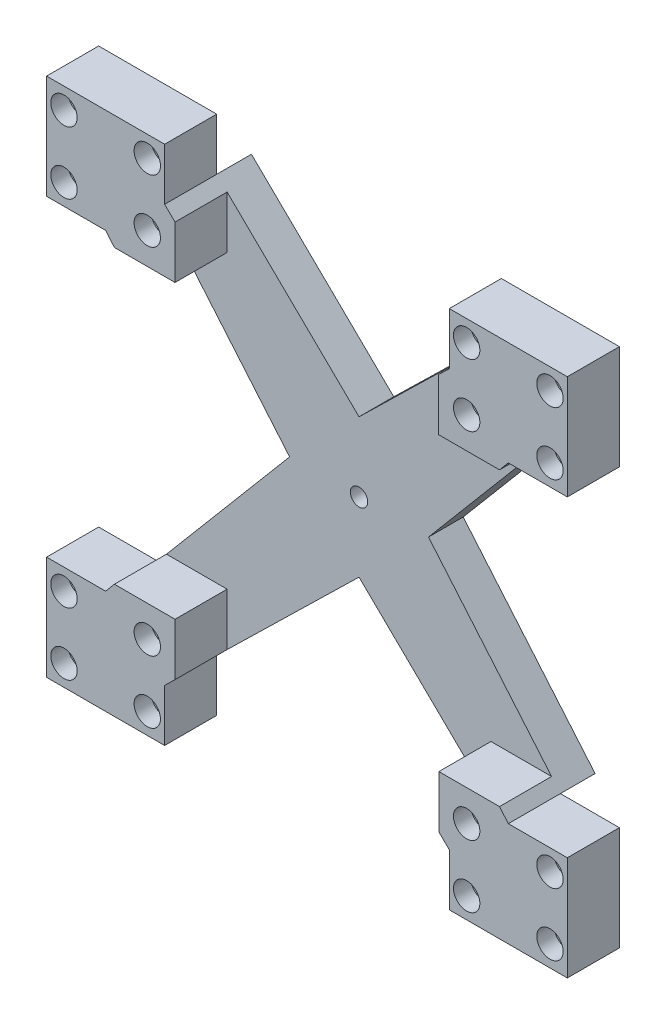
SolidWorks part; units mm, degrees
ref_plane "Front Plane" through (0, 0, 0) normal (0, 0, 1) x (1, 0, 0)
ref_plane "Top Plane" through (0, 0, 0) normal (0, 1, 0) x (1, 0, 0)
ref_plane "Right Plane" through (0, 0, 0) normal (1, 0, 0) x (0, 0, -1)
sketch "Sketch1" plane through (0, 0, 0) normal (0, 0, 1) x (1, 0, 0)
  line L1 (-75, -75) -> (75, -75)
  line L2 (-75, -75) -> (-75, 75)
  line L3 (-75, 75) -> (75, 75)
  line L4 (75, -75) -> (75, 75)
  line L5 (-75, -75) -> (75, 75) construction
  line L6 (-75, 75) -> (75, -75) construction
  point P0 (0, 0)
  dimension "D1" = 150
  dimension "D2" = 150
extrude "Boss-Extrude1" add sketch "Sketch1" along normal blind 15
sketch "Sketch2" plane through (0, 0, 15) normal (0, 0, 1) x (1, 0, 0)
  line L0 (-41, 60) -> (0, 20)
  line L1 (-75, 75) -> (-41, 75)
  line L2 (-75, 75) -> (-75, 45)
  line L3 (-75, 45) -> (-41, 45)
  line L4 (-41, 75) -> (-41, 45)
  line L5 (75, 75) -> (41, 75)
  line L6 (75, 75) -> (75, 45)
  line L7 (75, 45) -> (41, 45)
  line L8 (41, 75) -> (41, 45)
  line L9 (-75, -75) -> (-41, -75)
  line L10 (-75, -75) -> (-75, -45)
  line L11 (-75, -45) -> (-41, -45)
  line L12 (-41, -75) -> (-41, -45)
  line L13 (75, -75) -> (41, -75)
  line L14 (75, -75) -> (75, -45)
  line L15 (75, -45) -> (41, -45)
  line L16 (41, -75) -> (41, -45)
  line L17 (-20, -20) -> (20, -20)
  line L18 (-20, -20) -> (-20, 20)
  line L19 (-20, 20) -> (20, 20)
  line L20 (20, -20) -> (20, 20)
  line L21 (-20, -20) -> (20, 20) construction
  line L22 (-20, 20) -> (20, -20) construction
  line L23 (0, 20) -> (41, 60)
  line L24 (-58, -45) -> (-20, 0)
  line L25 (-20, 0) -> (-58, 45)
  line L26 (-41, -60) -> (0, -20)
  line L27 (0, -20) -> (41, -60)
  line L28 (58, 45) -> (20, 0)
  line L29 (20, 0) -> (58, -45)
  point P20 (0, 0)
  line M15 (75, -75) -> (75, 75)
  line M16 (75, 75) -> (-75, 75)
  line M17 (-75, 75) -> (-75, -75)
  line M18 (-75, -75) -> (75, -75)
  dimension "D1" = 34
  dimension "D2" = 30
  dimension "D3" = 34
  dimension "D4" = 30
  dimension "D5" = 30
  dimension "D6" = 30
  dimension "D7" = 34
  dimension "D8" = 34
  dimension "D9" = 40
  dimension "D10" = 40
extrude "Cut-Extrude1" cut sketch "Sketch2" against normal blind 15 contours L0 L23 L8 L4 M16 | L24 L25 L3 L11 M17 | L28 L29 L15 L7 M15 | L27 L26 L12 L16 M18
sketch "Sketch3" plane through (0, 0, 15) normal (0, 0, 1) x (1, 0, 0)
  line L0 (-58, 45.0694) -> (-20, 0)
  line L1 (-41, -75) -> (-75, -75)
  line L2 (-41, -75) -> (-41, -45)
  line L3 (-41, -45) -> (-75, -45)
  line L4 (-75, -75) -> (-75, -45)
  line L5 (-75, 75) -> (-41, 75)
  line L6 (-75, 75) -> (-75, 45.0694)
  line L7 (-75, 45.0694) -> (-41, 45.0694)
  line L8 (-41, 75) -> (-41, 45.0694)
  line L9 (75, 45) -> (41, 45)
  line L10 (75, 45) -> (75, 75)
  line L11 (75, 75) -> (41, 75)
  line L12 (41, 45) -> (41, 75)
  line L13 (41, -75) -> (75, -75)
  line L14 (41, -75) -> (41, -45)
  line L15 (41, -45) -> (75, -45)
  line L16 (75, -75) -> (75, -45)
  line L17 (-20, 0) -> (-58, -45)
  line L18 (-41, 60.0347) -> (0, 20)
  line L19 (0, 20) -> (41, 60)
  line L20 (58, 45) -> (20, 0)
  line L21 (20, 0) -> (58, -45)
  line L22 (41, -60) -> (0, -20)
  line L23 (0, -20) -> (-41, -60)
  line M9 (-20, 0) -> (-58, -45)
  line M14 (-41, -60) -> (0, -20)
  line M15 (0, -20) -> (41, -60)
  line M20 (58, -45) -> (20, 0)
  line M21 (20, 0) -> (58, 45)
  line M26 (41, 60) -> (0, 20)
  line M27 (0, 20) -> (-41, 60)
extrude "Boss-Extrude2" add sketch "Sketch3" against normal blind 25 contours L14 L15 L9 L12 L8 L7 L0 L3 L2 M20 M21 M26 M27 M9 M14 M15
sketch "Sketch4" plane through (0, 0, 15) normal (0, 0, 1) x (1, 0, 0)
  line L0 (-38, -57.0732) -> (-41, -60)
  line L1 (-75, 45) -> (-41, 45)
  line L2 (-75, 45) -> (-75, 75)
  line L3 (-75, 75) -> (-41, 75)
  line L4 (-41, 45) -> (-41, 75)
  line L5 (75, 45) -> (41, 45)
  line L6 (75, 45) -> (75, 75)
  line L7 (75, 75) -> (41, 75)
  line L8 (41, 45) -> (41, 75)
  line L9 (41, -75) -> (75, -75)
  line L10 (41, -75) -> (41, -45)
  line L11 (41, -45) -> (75, -45)
  line L12 (75, -75) -> (75, -45)
  line L13 (-41, -75) -> (-75, -75)
  line L14 (-41, -75) -> (-41, -45)
  line L15 (-41, -45) -> (-75, -45)
  line L16 (-75, -75) -> (-75, -45)
  line L17 (0, 20) -> (-37.2207, 56.3128)
  line L18 (-41, 60) -> (0, 20) construction
  line L19 (41, -60) -> (38, -57.0732)
  line L20 (-58, 45) -> (-55.4667, 42)
  line L21 (0, -20) -> (41, -60) construction
  line L22 (0, 20) -> (-37.4263, 56.5134)
  line L23 (38, -57.0732) -> (38, -42)
  line L24 (-58, -45) -> (-55.4667, -42)
  line L25 (-58, -45) -> (-20, 0) construction
  line L26 (-55.4667, -42) -> (-38, -42)
  line L27 (-38, -42) -> (-38, -57.0732)
  line L28 (-41, -60) -> (0, -20) construction
  line L29 (38, -42) -> (55.4667, -42)
  line L30 (20, 0) -> (58, -45) construction
  line L31 (55.4667, -42) -> (58, -45)
  line L32 (-20, 0) -> (-58, 45) construction
  line L33 (-55.4667, 42) -> (-38, 42)
  line L34 (-38, 42) -> (-38, 57.0732)
  line L35 (-38, 57.0732) -> (-41, 60)
  line L36 (41, 60) -> (37.925, 57)
  line L37 (0, 20) -> (41, 60) construction
  line L38 (37.925, 57) -> (37.925, 42)
  line L39 (37.925, 42) -> (55.4667, 42)
  line L40 (58, 45) -> (20, 0) construction
  line L41 (55.4667, 42) -> (58, 45)
  line M9 (0, -20) -> (41, -60)
  line M14 (58, -45) -> (20, 0)
  line M15 (20, 0) -> (58, 45)
  line M20 (41, 60) -> (0, 20)
  line M21 (0, 20) -> (-41, 60)
  line M26 (-58, 45) -> (-20, 0)
  line M27 (-20, 0) -> (-58, -45)
  line M32 (-41, -60) -> (0, -20)
  dimension "D1" = 3
  dimension "D2" = 3
  dimension "D3" = 3
  dimension "D4" = 3
  dimension "D5" = 3
  dimension "D6" = 3
  dimension "D7" = 3
  dimension "D8" = 3
extrude "Cut-Extrude2" cut sketch "Sketch4" against normal blind 15 contours L39 L38 L34 L33 L26 L27 L23 L29 M20 M21 M26 M27 M32 M9 M14 M15 | L6 L5 L8 L7
sketch "Sketch5" plane through (0, 0, 0) normal (0, 0, 1) x (1, 0, 0)
  circle A0 centre (0, 0) radius 2.5
  dimension "D1" = 5
extrude "Cut-Extrude3" cut sketch "Sketch5" against normal blind 15
sketch "Sketch7" plane through (0, 0, 15) normal (0, 0, 1) x (1, 0, 0)
  line L0 (75, -45) -> (58, -45) construction
  line L1 (75, -75) -> (75, -45) construction
  line L2 (41, -75) -> (75, -75) construction
  line L3 (41, -75) -> (41, -60) construction
  circle A0 centre (70, -51) radius 2.5
  circle A1 centre (46, -51) radius 2.5
  circle A2 centre (46, -69) radius 2.5
  circle A3 centre (70, -69) radius 2.5
  dimension "D1" = 5
  dimension "D2" = 5
  dimension "D3" = 5
  dimension "D4" = 5
  dimension "D5" = 6
  dimension "D6" = 5
  dimension "D7" = 5
  dimension "D8" = 6
  dimension "D9" = 5
  dimension "D10" = 6
  dimension "D11" = 6
  dimension "D12" = 5
extrude "Cut-Extrude4" cut sketch "Sketch7" against normal blind 15
sketch "Sketch8" plane through (0, 0, 15) normal (0, 0, 1) x (1, 0, 0)
  circle A0 centre (46, -51) radius 3.8
  circle A1 centre (70, -51) radius 3.8
  circle A2 centre (70, -69) radius 3.8
  circle A3 centre (46, -69) radius 3.8
  dimension "D1" = 7.6
  dimension "D2" = 7.6
  dimension "D3" = 7.6
  dimension "D4" = 7.6
extrude "Cut-Extrude5" cut sketch "Sketch8" against normal blind 5
sketch "Sketch10" plane through (0, 0, 15) normal (0, 0, 1) x (1, 0, 0)
  line L0 (-75, -75) -> (-41, -75) construction
  line L1 (-75, -45) -> (-75, -75) construction
  line L2 (-41, -75) -> (-41, -60) construction
  line L3 (-75, -45) -> (-58, -45) construction
  circle A0 centre (-46, -69) radius 2.5
  circle A1 centre (-46, -51) radius 2.5
  circle A2 centre (-70, -51) radius 2.5
  circle A3 centre (-70, -69) radius 2.5
  dimension "D1" = 5
  dimension "D2" = 5
  dimension "D3" = 5
  dimension "D4" = 5
  dimension "D5" = 6
  dimension "D6" = 5
  dimension "D7" = 6
  dimension "D8" = 5
  dimension "D10" = 5
  dimension "D11" = 5
  dimension "D12" = 6
  dimension "D9" = 6
extrude "Cut-Extrude6" cut sketch "Sketch10" against normal through all
sketch "Sketch11" plane through (0, 0, 15) normal (0, 0, 1) x (1, 0, 0)
  circle A0 centre (-70, -51) radius 3.8
  circle A1 centre (-46, -51) radius 3.8
  circle A2 centre (-70, -69) radius 3.8
  circle A3 centre (-46, -69) radius 3.8
  dimension "D1" = 7.6
  dimension "D2" = 7.6
  dimension "D3" = 7.6
  dimension "D4" = 7.6
extrude "Cut-Extrude7" cut sketch "Sketch11" against normal blind 5
sketch "Sketch12" plane through (0, 0, 15) normal (0, 0, 1) x (1, 0, 0)
  line L0 (75, 75) -> (41, 75) construction
  line L1 (75, 45) -> (75, 75) construction
  line L2 (75, 45) -> (58, 45) construction
  line L3 (41, 75) -> (41, 60) construction
  circle A0 centre (46, 69) radius 2.5
  circle A1 centre (70, 69) radius 2.5
  circle A2 centre (70, 51) radius 2.5
  circle A3 centre (46, 51) radius 2.5
  dimension "D1" = 5
  dimension "D2" = 5
  dimension "D3" = 5
  dimension "D4" = 5
  dimension "D5" = 6
  dimension "D6" = 5
  dimension "D7" = 6
  dimension "D8" = 5
  dimension "D9" = 6
  dimension "D10" = 5
  dimension "D11" = 6
  dimension "D12" = 5
extrude "Cut-Extrude8" cut sketch "Sketch12" against normal through all
sketch "Sketch13" plane through (0, 0, 15) normal (0, 0, 1) x (1, 0, 0)
  circle A0 centre (70, 69) radius 3.8
  circle A1 centre (46, 69) radius 3.8
  circle A2 centre (46, 51) radius 3.8
  circle A3 centre (70, 51) radius 3.8
  dimension "D1" = 7.6
  dimension "D2" = 7.6
  dimension "D3" = 7.6
  dimension "D4" = 7.6
extrude "Cut-Extrude9" cut sketch "Sketch13" against normal blind 5
sketch "Sketch14" plane through (0, 0, 15) normal (0, 0, 1) x (1, 0, 0)
  line L0 (-75, 45) -> (-58, 45) construction
  line L1 (-41, 75) -> (-41, 60) construction
  line L2 (-41, 75) -> (-75, 75) construction
  line L3 (-75, 75) -> (-75, 45) construction
  circle A0 centre (-70, 69) radius 2.5
  circle A1 centre (-46, 69) radius 2.5
  circle A2 centre (-46, 51) radius 2.5
  circle A3 centre (-70, 51) radius 2.5
  dimension "D1" = 5
  dimension "D2" = 5
  dimension "D3" = 5
  dimension "D4" = 5
  dimension "D5" = 6
  dimension "D6" = 6
  dimension "D7" = 5
  dimension "D8" = 5
  dimension "D10" = 6
  dimension "D11" = 5
  dimension "D12" = 5
  dimension "D9" = 6
extrude "Cut-Extrude10" cut sketch "Sketch14" against normal through all
sketch "Sketch15" plane through (0, 0, 15) normal (0, 0, 1) x (1, 0, 0)
  circle A0 centre (-70, 69) radius 3.8
  circle A1 centre (-46, 69) radius 3.8
  circle A2 centre (-46, 51) radius 3.8
  circle A3 centre (-70, 51) radius 3.8
  dimension "D1" = 7.6
  dimension "D2" = 7.6
  dimension "D3" = 7.6
  dimension "D4" = 7.6
extrude "Cut-Extrude11" cut sketch "Sketch15" against normal blind 5
